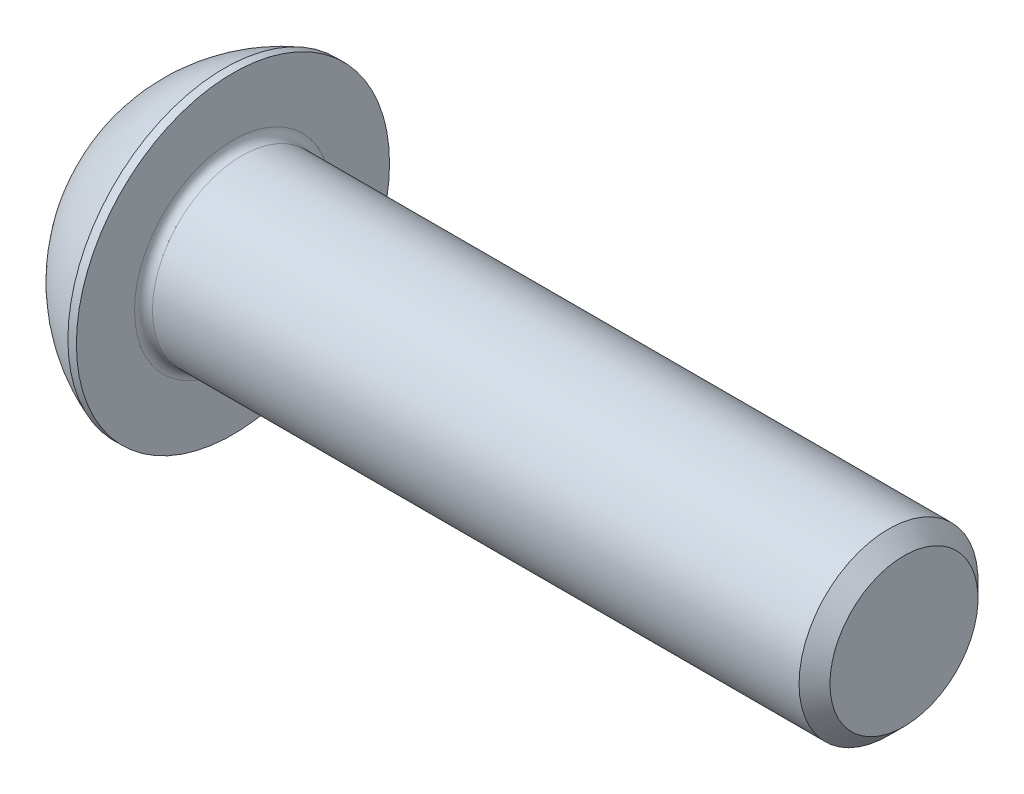
SolidWorks part; units mm, degrees
ref_plane "Plane1" through (0, 0, 0) normal (0, 0, 1) x (1, 0, 0)
ref_plane "Plane2" through (0, 0, 0) normal (0, 1, 0) x (1, 0, 0)
ref_plane "Plane3" through (0, 0, 0) normal (1, 0, 0) x (0, 0, -1)
sketch "BodySke" plane through (0, 0, 0) normal (0, 0, 1) x (1, 0, 0)
  line L0 (34.4, 0) -> (34.4, 3.3095)
  line L1 (33.7095, 4) -> (4.4, 4)
  line L2 (4.4, 4) -> (4.4, 7)
  line L3 (4.4, 7) -> (4.02, 7)
  line L4 (0, 0) -> (101.6, 0) construction
  line L5 (4.4, -7) -> (4.02, -7) construction
  line L6 (55.6768, -4) -> (4.4, -4) construction
  line L7 (34.4, 0) -> (0, 0)
  line L8 (0, 3.5) -> (0, -3.5) construction
  line L9 (0, 0) -> (0, 3.5)
  line L10 (34.4, 3.3095) -> (33.7095, 4)
  line L11 (34.4, -3.3095) -> (33.7095, -4) construction
  line L12 (5.65, 9.525) -> (5.65, -4) construction
  line L13 (4.4, 9.525) -> (4.4, -4) construction
  arc A1 (0, 3.5) -> (4.02, 7) centre (6.5809, 0) cw
  dimension "D1" = 7
  dimension "Diameter" = 8
  dimension "Length" = 30
  dimension "Head_dia" = 14
  dimension "Head_ht" = 4.4
  dimension "Head_side_ht" = 0.38
  dimension "Minor_dia" = 6.619
  dimension "Body_ch_ang" = 45
  dimension "Advance" = 1.25
  dimension "Thread_nom" = 30
revolve "BaseBody" add sketch "BodySke" angle 360 about L4
cosmetic thread "ThreadCosmetic" [suppressed] parameters "Thread_length"=27.5, "Thread_minor"=6.619
fillet "Fillet1" radius 0.4 1 edges at (4.4, 0, 4)
sketch "Sketch2" plane through (0, 0, 0) normal (0, 0, 1) x (1, 0, 0)
  line L0 (0, 2.5) -> (2.6, 2.5)
  line L1 (2.6, 2.5) -> (4.0434, 0)
  line L3 (4.0434, 0) -> (0, 0)
  line L4 (0, 0) -> (0, 2.5)
  line L5 (0, -2.5) -> (2.6, -2.5) construction
  line L6 (0, 0) -> (47.625, 0) construction
  dimension "D2" = 60
  dimension "PreBroach_depth" = 2.6
  dimension "PreBroach_dia" = 5
revolve "PreBroach" cut sketch "Sketch2" angle 360 about L6
sketch "Sketch3" plane through (0, 0, 0) normal (1, 0, 0) x (0, 0, -1)
  line L0 (-2.5, -1.4434) -> (-2.5, 1.4434)
  line L1 (-2.5, 1.4434) -> (0, 2.8868)
  line L2 (0, 2.8868) -> (2.5, 1.4434)
  line L3 (2.5, 1.4434) -> (2.5, -1.4434)
  line L4 (2.5, -1.4434) -> (0, -2.8868)
  line L5 (0, -2.8868) -> (-2.5, -1.4434)
  dimension "D1" = 2.5
  dimension "D2" = 2.5
  dimension "D3" = 5
  dimension "Hex_size" = 5
extrude "Hex" cut sketch "Sketch3" along normal blind 2.6
sketch "ThdSchSke" plane through (0, 0, 0) normal (0, 0, 1) x (1, 0, 0)
  line L0 (6.9, -3.3095) -> (6.4165, -4)
  line L1 (6.9, -3.3095) -> (7.3835, -4)
  line L2 (7.3835, -4) -> (7.3835, -5)
  line L3 (-3.175, 0) -> (5.1513, 0) construction
  line L5 (7.3835, -5) -> (6.4165, -5)
  line L6 (6.4165, -5) -> (6.4165, -4)
  dimension "Thread_minor" = 6.619
  dimension "Diameter" = 8
  dimension "Start" = 6.9
  dimension "SideAngle" = 55
  dimension "VeeAngle" = 70
  dimension "Overcut" = 10
revolve "ThreadSchematic" [suppressed] cut sketch "ThdSchSke" angle 360 about L3
pattern_linear "ThdSchPat" [suppressed]
equation "\"D1@BodySke\" = \"Head_dia@BodySke\" * .5"
equation "\"Thread_minor@ThreadCosmetic\" = \"Minor_dia@BodySke\""
equation "\"D1@Sketch3\" = \"Hex_size@Sketch3\" / 2"
equation "\"D2@Sketch3\" = \"D1@Sketch3\""
equation "\"D3@Sketch3\" = \"Hex_size@Sketch3\""
equation "\"Thread_length@ThreadCosmetic\" = ((sgn( (\"Length@BodySke\" - \"Advance@BodySke\" * 2.0) - \"Thread_nom@BodySke\" )-1)*( (\"Length@BodySke\" - \"Advance@BodySke\" * 2.0) - \"Thread_nom@BodySke\" ))/-2+ \"Thread_nom@BodySke\""
equation "\"Thread_minor@ThdSchSke\" = \"Minor_dia@BodySke\""
equation "\"Diameter@ThdSchSke\" = \"Diameter@BodySke\""
equation "\"Overcut@ThdSchSke\" = \"Diameter@BodySke\" * 1.25"
equation "\"Start@ThdSchSke\" = \"Head_ht@BodySke\" + \"Length@BodySke\" - \"Thread_length@ThreadCosmetic\"  '---Non-countersunk---"
equation "\"Num_threads@ThdSchPat\" = int( \"Thread_length@ThreadCosmetic\" / \"Advance@BodySke\" + 0.999 )  + 1"
equation "\"Advance@ThdSchPat\" = \"Thread_length@ThreadCosmetic\" /  (\"Num_threads@ThdSchPat\" - 1) 'relax it"
equation "\"Num_threads@ThdSchPat\" = \"Num_threads@ThdSchPat\" - sgn( \"Num_threads@ThdSchPat\" - 1) '---chamfered tips only---"
